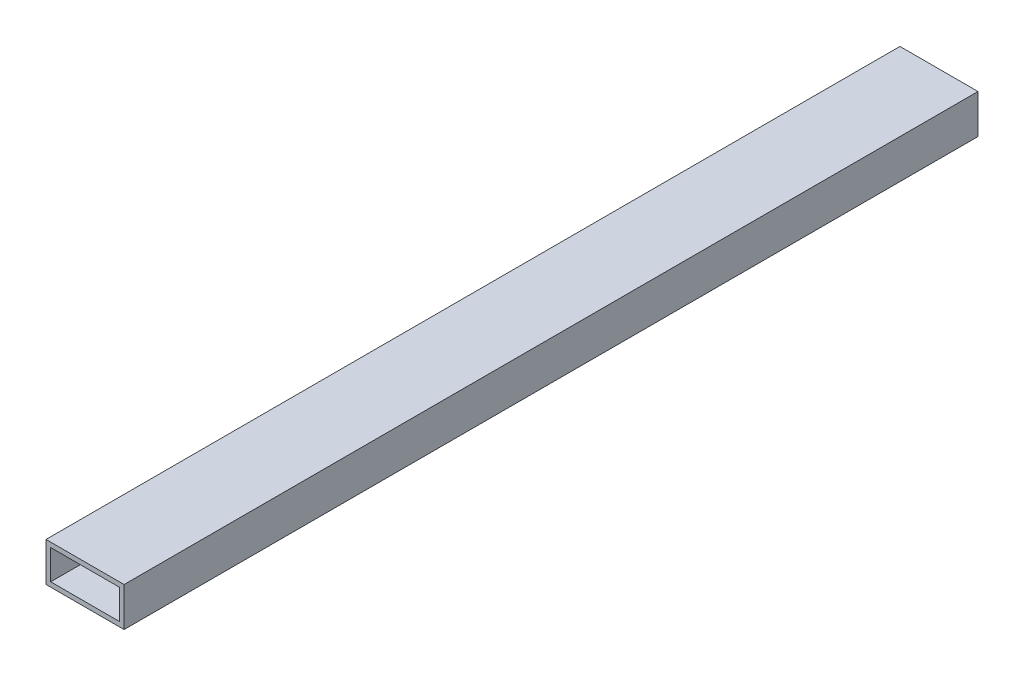
SolidWorks part; units mm, degrees
ref_plane "Front Plane" through (0, 0, 0) normal (0, 0, 1) x (1, 0, 0)
ref_plane "Top Plane" through (0, 0, 0) normal (0, 1, 0) x (1, 0, 0)
ref_plane "Right Plane" through (0, 0, 0) normal (1, 0, 0) x (0, 0, -1)
sketch "Sketch1" plane through (0, 0, 0) normal (0, 0, 1) x (1, 0, 0)
  line L0 (3.048, 3.048) -> (3.048, 22.352)
  line L1 (0, 0) -> (50.8, 0)
  line L2 (0, 0) -> (0, 25.4)
  line L3 (0, 25.4) -> (50.8, 25.4)
  line L4 (50.8, 0) -> (50.8, 25.4)
  line L5 (3.048, 22.352) -> (47.752, 22.352)
  line L6 (47.752, 3.048) -> (47.752, 22.352)
  line L7 (3.048, 3.048) -> (47.752, 3.048)
  dimension "D1" = 50.8
  dimension "D2" = 25.4
  dimension "D3" = 3.048
extrude "Boss-Extrude1" add sketch "Sketch1" along normal blind 555.625 from offset 3.175
